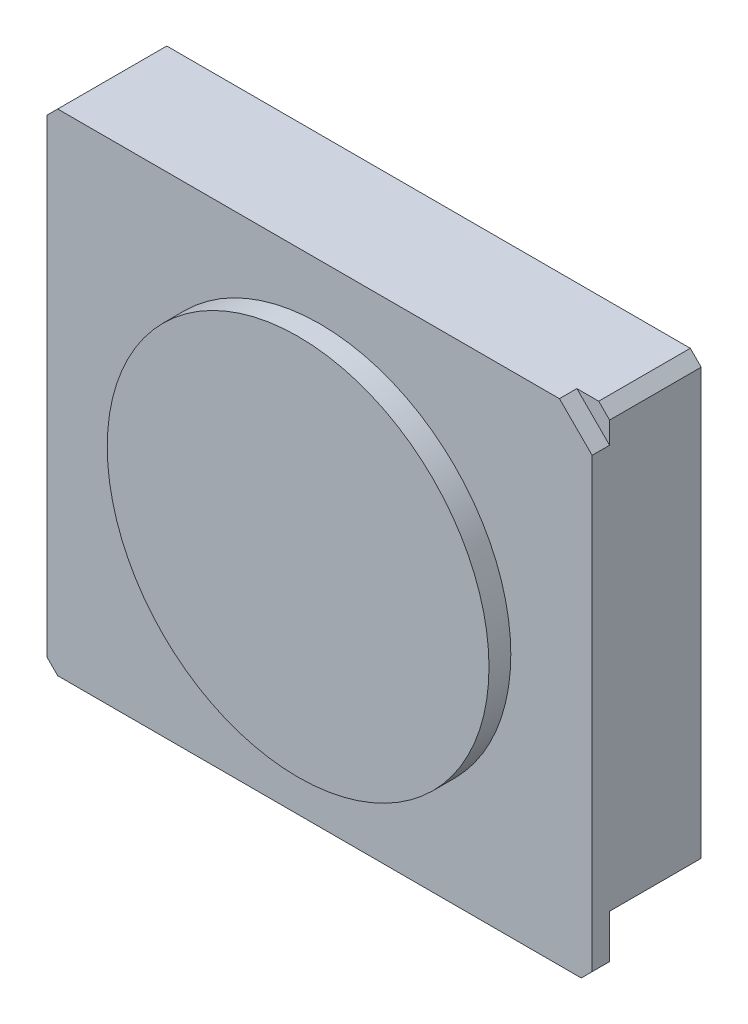
SolidWorks part; units mm, degrees
ref_plane "前视基准面" through (0, 0, 0) normal (0, 0, 1) x (1, 0, 0)
ref_plane "上视基准面" through (0, 0, 0) normal (0, 1, 0) x (1, 0, 0)
ref_plane "右视基准面" through (0, 0, 0) normal (1, 0, 0) x (0, 0, -1)
sketch "草图1" plane through (0, 0, 0) normal (0, 0, 1) x (1, 0, 0)
  line L0 (21.957, 22.5387) -> (24.957, 19.5387)
  line L1 (-25.043, -22.4613) -> (24.957, -22.4613)
  line L2 (-25.043, -22.4613) -> (-25.043, 22.5387)
  line L3 (-25.043, 22.5387) -> (21.957, 22.5387)
  line L4 (24.957, -22.4613) -> (24.957, 19.5387)
  line L5 (-25.043, -22.4613) -> (23.457, 21.0387) construction
  line L6 (-25.043, 22.5387) -> (24.957, -22.4613) construction
  point P0 (0, 0)
  dimension "D1" = 50
  dimension "D2" = 45
  dimension "D3" = 3
  dimension "D4" = 3
extrude "凸台-拉伸1" add sketch "草图1" against normal blind 1.6
sketch "草图2" plane through (0, 0, 0) normal (0, 0, 1) x (1, 0, 0)
  circle A0 centre (0, 0) radius 17.5
  dimension "D1" = 35
extrude "凸台-拉伸2" add sketch "草图2" along normal blind 2
sketch "草图3" plane through (0, 0, -1.6) normal (0, 0, -1) x (-1, 0, 0)
  line L0 (-24.957, -22.4613) -> (-24.957, 19.5387) construction
  line L1 (25.043, 22.5387) -> (-24.957, 22.5387)
  line L2 (25.043, 22.5387) -> (25.043, -17.4613)
  line L3 (25.043, -17.4613) -> (-24.957, -17.4613)
  line L4 (-24.957, 22.5387) -> (-24.957, -17.4613)
  dimension "D1" = 40
extrude "凸台-拉伸3" add sketch "草图3" along normal blind 8.4
sketch "草图4" plane through (0, -17.4613, 0) normal (0, -1, 0) x (1, 0, 0)
  line L0 (-2.9, -4.9) -> (2.9, -4.9) construction
  line L1 (-2.9, -3.3) -> (2.9, -3.3)
  line L2 (-2.9, -6.5) -> (2.9, -6.5)
  line L3 (-25.043, -1.6) -> (24.957, -1.6) construction
  arc A0 (-2.9, -3.3) -> (-2.9, -6.5) centre (-2.9, -4.9) ccw
  arc A1 (2.9, -6.5) -> (2.9, -3.3) centre (2.9, -4.9) ccw
  point P2 (0, -4.9)
  point P9 (4.5, -4.9)
  point P10 (-4.5, -4.9)
  dimension "D3" = 9
  dimension "D1" = 1.7
  dimension "D2" = 3.2
extrude "凸台-拉伸4" add sketch "草图4" along normal offset from surface (5.3 mm away) 0.3 up to face at (-0.043, -22.4613, -0.8) offset beyond the face yes
sketch "草图5" plane through (0, 0, -1.6) normal (0, 0, -1) x (-1, 0, 0)
  line L1 (15.543, -21.4613) -> (18.443, -21.4613)
  line L2 (15.543, -21.4613) -> (15.543, -23.4613)
  line L3 (15.543, -23.4613) -> (18.443, -23.4613)
  line L4 (18.443, -21.4613) -> (18.443, -23.4613)
  line L5 (25.043, -17.4613) -> (25.043, -22.4613) construction
  line L6 (25.043, -22.4613) -> (-24.957, -22.4613) construction
  dimension "D1" = 9.5
  dimension "D2" = 6.6
  dimension "D3" = 1
  dimension "D4" = 1
extrude "凸台-拉伸5" add sketch "草图5" along normal blind 1.5
chamfer "倒角1" distance 1 angle 45 4 edges at (-25.043, 22.5387, -5) (24.957, 22.5387, -5.8) (24.957, -22.4613, -0.8) (-25.043, -22.4613, -0.8)
